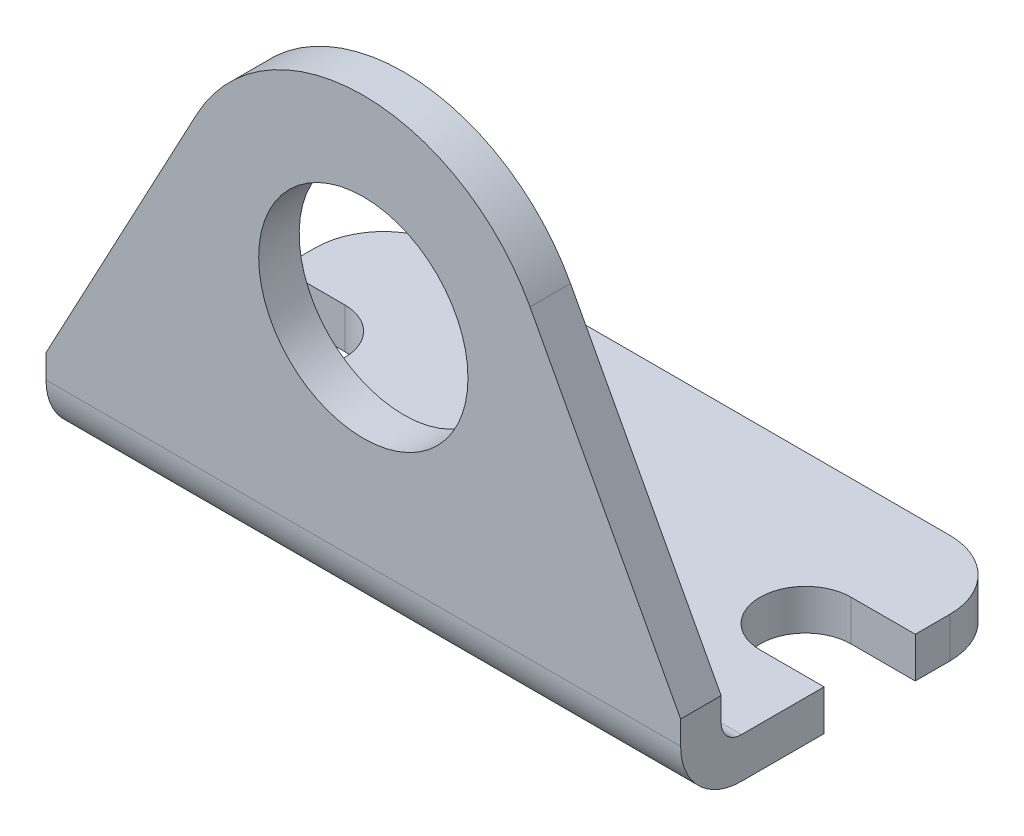
SolidWorks part; units mm, degrees
ref_plane "Front Plane" through (0, 0, 0) normal (0, 0, 1) x (1, 0, 0)
ref_plane "Top Plane" through (0, 0, 0) normal (0, 1, 0) x (1, 0, 0)
ref_plane "Right Plane" through (0, 0, 0) normal (1, 0, 0) x (0, 0, -1)
sketch "Sketch1" plane through (0, 0, 0) normal (0, 1, 0) x (1, 0, 0)
  line L0 (-23.876, 0) -> (23.876, 0) construction
  line L1 (0, 11.176) -> (0, -14.224) construction
  line L2 (-19.05, 3.429) -> (-23.876, 3.429)
  line L3 (-23.876, 3.429) -> (-23.876, -3.429)
  line L4 (-19.05, -3.429) -> (-23.876, -3.429)
  line L5 (19.05, 3.429) -> (23.876, 3.429)
  line L6 (23.876, 3.429) -> (23.876, -3.429)
  line L7 (19.05, -3.429) -> (23.876, -3.429)
  arc A0 (-19.05, -3.429) -> (-19.05, 3.429) centre (-19.05, 0) ccw
  arc A1 (19.05, 3.429) -> (19.05, -3.429) centre (19.05, 0) ccw
  dimension "Width" = 47.752
  dimension "Depth" = 25.4
  dimension "Hole Dia" = 6.858
  dimension "Hole Location" = 19.05
  dimension "D5" = 19.05
  dimension "HL" = 14.224
sketch "Sketch2" plane through (0, 0, 0) normal (0, 0, 1) x (1, 0, 0)
  line L0 (-23.876, 0) -> (23.876, 0)
  line L1 (23.876, 0) -> (23.876, 6.35)
  line L2 (23.876, 6.35) -> (12.5423, 27.5373)
  line L3 (-23.876, 0) -> (-23.876, 6.35)
  line L4 (-23.876, 6.35) -> (-12.5423, 27.5373)
  line L5 (0, 0) -> (0, 20.828) construction
  line L6 (-23.876, 3.048) -> (23.876, 3.048) construction
  arc A0 (-12.5423, 27.5373) -> (12.5423, 27.5373) centre (0, 20.828) cw
  circle A1 centre (0, 20.574) radius 7.874
  dimension "Thickness" = 3.048
  dimension "ID" = 15.748
  dimension "Radius" = 14.224
  dimension "C to C" = 20.574
  dimension "Height" = 35.052
  dimension "D5" = 6.35
sketch "Sketch3" plane through (0, 0, 0) normal (0, 0, 1) x (1, 0, 0)
  line L5 (-23.876, 0) -> (23.876, 0)
  line L6 (23.876, 0) -> (23.876, 6.35)
  line L7 (23.876, 6.35) -> (12.5423, 27.5373)
  line L8 (-12.5423, 27.5373) -> (-23.876, 6.35)
  line L9 (-23.876, 6.35) -> (-23.876, 0)
  line L10 (-23.876, 0) -> (23.876, 0)
  line L11 (23.876, 0) -> (23.876, 6.35)
  line L12 (23.876, 6.35) -> (12.5423, 27.5373)
  line L13 (-12.5423, 27.5373) -> (-23.876, 6.35)
  line L14 (-23.876, 6.35) -> (-23.876, 0)
  circle A1 centre (0, 20.574) radius 7.874
  circle A2 centre (0, 20.574) radius 7.874
  arc A3 (12.5423, 27.5373) -> (-12.5423, 27.5373) centre (0, 20.828) ccw
  arc A4 (12.5423, 27.5373) -> (-12.5423, 27.5373) centre (0, 20.828) ccw
  dimension "D1" = 0
  dimension "D2" = 0
extrude "Boss-Extrude1" add sketch "Sketch3" along normal up to vertex (14.224 mm away) and the other way up to vertex (11.176 mm away) up to point (0, 0, 14.224) other way up to point (0, 0, -11.176)
sketch "Sketch4" plane through (0, 0, 0) normal (0, 1, 0) x (1, 0, 0)
  line L0 (-23.876, 3.429) -> (-23.876, -3.429) construction
  line L1 (-19.05, -3.429) -> (-23.876, -3.429) construction
  line L2 (-19.05, 3.429) -> (-23.876, 3.429) construction
  line L3 (19.05, 3.429) -> (23.876, 3.429) construction
  line L4 (19.05, -3.429) -> (23.876, -3.429) construction
  line L6 (-23.876, 3.429) -> (-23.876, -3.429)
  line L7 (-19.05, -3.429) -> (-23.876, -3.429)
  line L8 (-19.05, 3.429) -> (-23.876, 3.429)
  line L9 (19.05, 3.429) -> (23.876, 3.429)
  line L10 (19.05, -3.429) -> (23.876, -3.429)
  line L12 (23.876, -3.429) -> (23.876, 3.429)
  arc A0 (-19.05, -3.429) -> (-19.05, 3.429) centre (-19.05, 0) ccw construction
  arc A1 (19.05, 3.429) -> (19.05, -3.429) centre (19.05, 0) ccw construction
  arc A2 (-19.05, -3.429) -> (-19.05, 3.429) centre (-19.05, 0) ccw
  arc A3 (19.05, 3.429) -> (19.05, -3.429) centre (19.05, 0) ccw
extrude "Cut-Extrude1" cut sketch "Sketch4" along normal through all
sketch "Sketch5" plane through (-23.876, 0, 0) normal (-1, 0, 0) x (0, 0, 1)
  line L0 (14.224, 27.5373) -> (14.224, 6.35) construction
  line L1 (-11.176, 35.052) -> (11.176, 35.052)
  line L2 (-11.176, 35.052) -> (-11.176, 3.048)
  line L3 (-11.176, 3.048) -> (9.652, 3.048)
  line L4 (11.176, 35.052) -> (11.176, 4.572)
  line L5 (-11.176, 6.35) -> (-11.176, 0) construction
  line L6 (14.224, 35.052) -> (-11.176, 35.052) construction
  line L7 (-11.176, 0) -> (14.224, 0) construction
  line L8 (14.224, 6.35) -> (14.224, 0) construction
  line L9 (9.652, 0) -> (14.224, 0)
  line L10 (14.224, 4.572) -> (14.224, 0)
  arc A0 (9.652, 3.048) -> (11.176, 4.572) centre (9.652, 4.572) ccw
  arc A1 (9.652, 0) -> (14.224, 4.572) centre (9.652, 4.572) ccw
  dimension "D3" = 1.524
  dimension "D4" = 4.572
  dimension "D1" = 3.048
  dimension "Thickness" = 3.048
extrude "Cut-Extrude2" cut sketch "Sketch5" against normal through all
fillet "Fillet1" radius 5.1435 2 edges at (-23.876, 1.524, -11.176) (23.876, 1.524, -11.176)
equation "\"D4@Sketch5\" = \"D1@Sketch5\"+\"D3@Sketch5\""
equation "\"D5@Sketch1\" = \"Hole Location@Sketch1\""
equation "\"D3@Sketch5\" = \"Thickness@Sketch5\"/2"
equation "\"D1@Fillet1\" = \"Hole Dia@Sketch1\"*.750"
equation "\"Thickness@Sketch5\" = \"Thickness@Sketch2\""
equation "\"D1@Sketch5\" = \"Thickness@Sketch5\""
